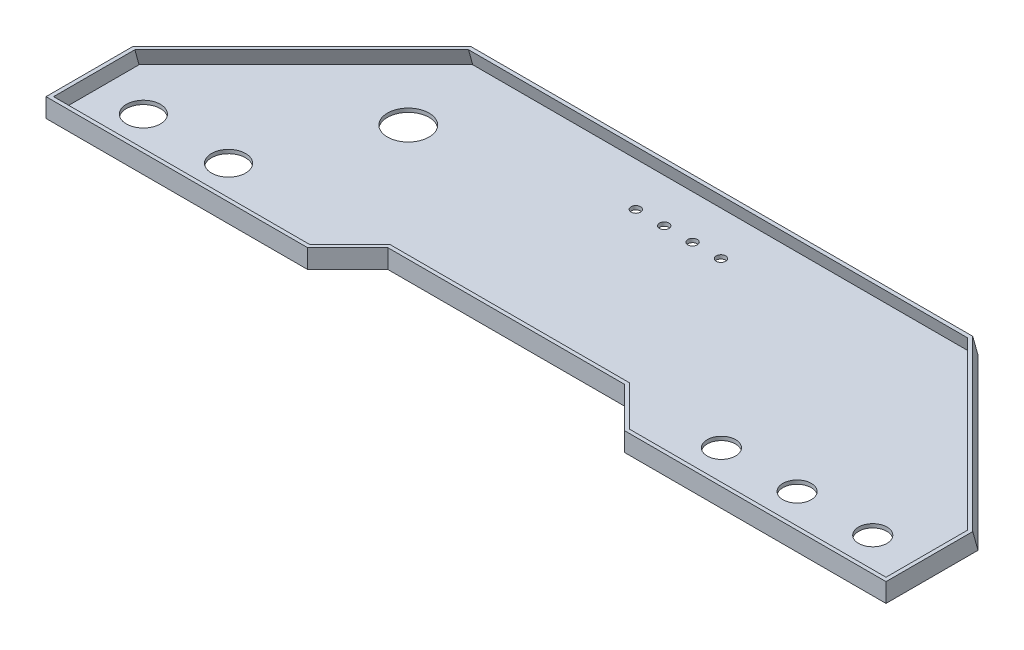
SolidWorks part; units mm, degrees
material "Thornel Mat VMA"
ref_plane "Front Plane" through (0, 0, 0) normal (0, 0, 1) x (1, 0, 0)
ref_plane "Top Plane" through (0, 0, 0) normal (0, 1, 0) x (1, 0, 0)
ref_plane "Right Plane" through (0, 0, 0) normal (1, 0, 0) x (0, 0, -1)
sketch "Sketch1" plane through (0, 0, 0) normal (0, 1, 0) x (1, 0, 0)
  line L0 (-135.1127, 0) -> (135.1127, 0) construction
  line L1 (-135.1127, 0) -> (-228, -92.8873) construction
  line L2 (-228, -92.8873) -> (-228, -150) construction
  line L3 (-228, -150) -> (-81.2132, -150) construction
  line L4 (-81.2132, -150) -> (-60, -128.7868) construction
  line L5 (-60, -128.7868) -> (60, -128.7868) construction
  line L6 (60, -128.7868) -> (81.2132, -150) construction
  line L7 (81.2132, -150) -> (228, -150) construction
  line L8 (135.1127, 0) -> (228, -92.8873) construction
  line L9 (228, -92.8873) -> (228, -150) construction
  line L10 (-132.6274, -6) -> (132.6274, -6)
  line L11 (132.6274, -6) -> (222, -95.3726)
  line L12 (222, -95.3726) -> (222, -144)
  line L13 (83.6985, -144) -> (222, -144)
  line L14 (62.4853, -122.7868) -> (83.6985, -144)
  line L15 (-62.4853, -122.7868) -> (62.4853, -122.7868)
  line L16 (-83.6985, -144) -> (-62.4853, -122.7868)
  line L17 (-222, -144) -> (-83.6985, -144)
  line L18 (-222, -95.3726) -> (-222, -144)
  line L19 (-132.6274, -6) -> (-222, -95.3726)
  point P3 (-220.9497, -56.6631)
  dimension "D1" = 120
  dimension "D2" = 30
  dimension "D3" = 150
  dimension "D4" = 270.2254
  dimension "D5" = 131.3625
  dimension "D6" = 6
ref_plane "Plane1" through (0, 10, 0) normal (0, 1, 0) x (1, 0, 0)
sketch "Sketch2" plane through (0, 10, 0) normal (0, 1, 0) x (1, 0, 0)
  line L0 (-83.6985, -144) -> (-62.4853, -122.7868)
  line L1 (-222, -144) -> (-83.6985, -144)
  line L2 (83.6985, -144) -> (222, -144)
  line L3 (-62.4853, -122.7868) -> (62.4853, -122.7868)
  line L4 (62.4853, -122.7868) -> (83.6985, -144)
  line L5 (132.6274, -8.7767) -> (-132.6274, -8.7767)
  line L6 (132.6274, -8.7767) -> (222, -98.1493)
  line L7 (-132.6274, -8.7767) -> (-222, -98.1493)
  line L8 (222, -144) -> (222, -98.1493)
  line L9 (-222, -144) -> (-222, -98.1493)
  line L10 (-222, -95.3726) -> (-222, -144) construction
  line L11 (-222, -144) -> (-83.6985, -144) construction
  point P10 (0, 0)
  point P11 (0, 0)
  point P12 (-199.6757, -113.3134)
  point P13 (0, 0)
  point P14 (-110.3031, -23.9408)
  point P15 (0, 0)
  point P17 (0, 0)
  point P18 (0, 0)
  point P19 (0, 0)
  point P20 (0, 0)
  point P22 (0, 0)
  dimension "D1" = 135
  dimension "D2" = 265.2548
  dimension "D3" = 126.3919
  dimension "D4" = 30
  dimension "D5" = 135
  dimension "D6" = 124.9706
  dimension "D7" = 45.8507
  dimension "D8" = 135
  dimension "D9" = 138.3015
loft "Loft2" add profiles "Sketch1", "Sketch2"
shell "Shell1" thickness 2
sketch "Sketch4" plane through (0, 0, 0) normal (0, -1, 0) x (1, 0, 0)
  line L0 (7.5, 31.74) -> (-7.5, 31.74) construction
  line L1 (132.6274, 6) -> (-132.6274, 6) construction
  line L2 (222, 144) -> (222, 95.3726) construction
  line L3 (83.6985, 144) -> (222, 144) construction
  line L4 (-222, 95.3726) -> (-222, 144) construction
  line L5 (-222, 144) -> (-83.6985, 144) construction
  circle A0 centre (22.5, 31.74) radius 2.5
  circle A1 centre (7.5, 31.74) radius 2.5
  circle A2 centre (-7.5, 31.74) radius 2.5
  circle A3 centre (-22.5, 31.74) radius 2.5
  circle A4 centre (189.26, 118.26) radius 7.5
  circle A5 centre (149.26, 118.26) radius 7.5
  circle A6 centre (109.26, 118.26) radius 7.5
  circle A7 centre (-151.26, 118.26) radius 9
  circle A8 centre (-196.26, 118.26) radius 9
  circle A9 centre (-121.26, 53.26) radius 11
  point P11 (0, 31.74)
  point P12 (0, 6)
  dimension "D4" = 5
  dimension "D8" = 15
  dimension "D12" = 18
  dimension "D13" = 25.74
  dimension "D14" = 90.74
  dimension "D16" = 22
  dimension "D1" = 15
  dimension "D2" = 15
  dimension "D3" = 15
  dimension "D5" = 25.74
  dimension "D6" = 32.74
  dimension "D7" = 25.74
  dimension "D9" = 40
  dimension "D10" = 40
  dimension "D11" = 45
  dimension "D15" = 100.74
extrude "Cut-Extrude1" cut sketch "Sketch4" against normal up to surface (10 mm away) up to face at (0, 10, 102.9342)
